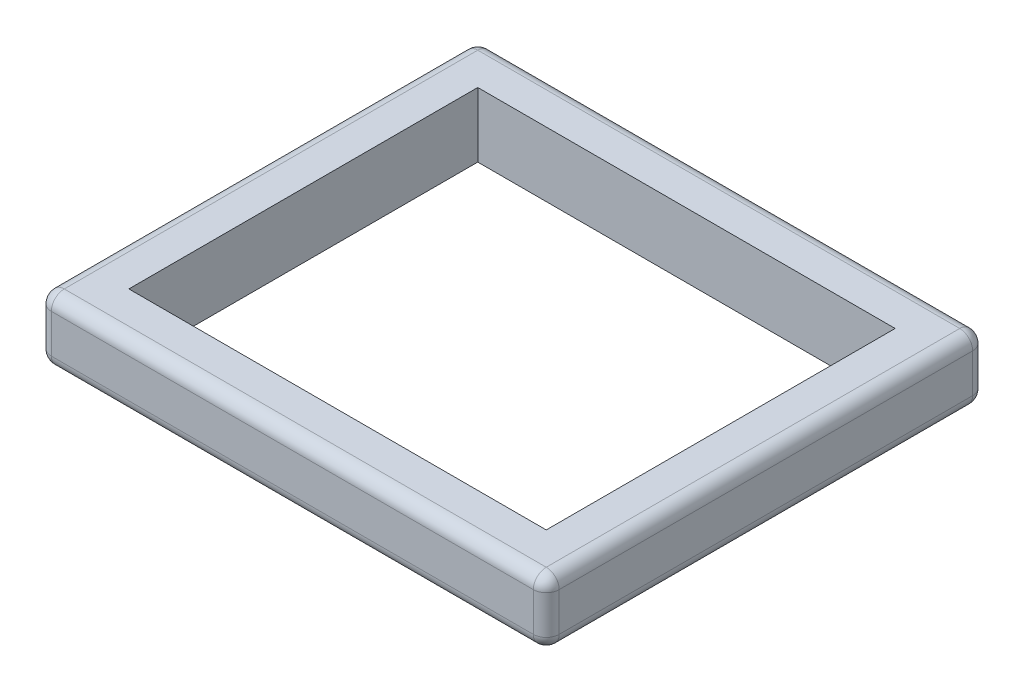
SolidWorks part; units mm, degrees
ref_plane "Front Plane" through (0, 0, 0) normal (0, 0, 1) x (1, 0, 0)
ref_plane "Top Plane" through (0, 0, 0) normal (0, 1, 0) x (1, 0, 0)
ref_plane "Right Plane" through (0, 0, 0) normal (1, 0, 0) x (0, 0, -1)
sketch "Sketch1" plane through (0, 0, 0) normal (0, 1, 0) x (1, 0, 0)
  line L0 (-272.9868, -413.7434) -> (-272.9868, 449.8566)
  line L1 (636.3332, -324.8434) -> (-184.0868, -324.8434)
  line L2 (636.3332, -324.8434) -> (636.3332, 360.9566)
  line L3 (636.3332, 360.9566) -> (-184.0868, 360.9566)
  line L4 (-184.0868, -324.8434) -> (-184.0868, 360.9566)
  line L5 (636.3332, -324.8434) -> (-184.0868, 360.9566) construction
  line L6 (636.3332, 360.9566) -> (-184.0868, -324.8434) construction
  line L7 (725.2332, 449.8566) -> (-272.9868, 449.8566)
  line L8 (725.2332, -413.7434) -> (725.2332, 449.8566)
  line L9 (725.2332, -413.7434) -> (-272.9868, -413.7434)
  point P0 (226.1232, 18.0566)
  dimension "D1" = 685.8
  dimension "D2" = 820.42
  dimension "D3" = 88.9
extrude "Boss-Extrude1" add sketch "Sketch1" along normal blind 127 contours L0 L7 L8 L9
sketch "Sketch2" plane through (0, 0, 0) normal (0, -1, 0) x (1, 0, 0)
  line L0 (725.2332, -449.8566) -> (-272.9868, -449.8566) construction
  line L1 (636.3332, -360.9566) -> (-184.0868, -360.9566)
  line L2 (636.3332, -360.9566) -> (636.3332, 324.8434)
  line L3 (636.3332, 324.8434) -> (-184.0868, 324.8434)
  line L4 (-184.0868, -360.9566) -> (-184.0868, 324.8434)
  line L5 (636.3332, -360.9566) -> (-184.0868, 324.8434) construction
  line L6 (636.3332, 324.8434) -> (-184.0868, -360.9566) construction
  line L7 (725.2332, 413.7434) -> (-272.9868, 413.7434) construction
  line L8 (-272.9868, 413.7434) -> (-272.9868, -449.8566) construction
  line L9 (725.2332, 413.7434) -> (725.2332, -449.8566) construction
  point P0 (226.1232, -18.0566)
  dimension "D1" = 88.9
  dimension "D2" = 88.9
  dimension "3" = 88.9
  dimension "D3" = 88.9
extrude "Cut-Extrude1" cut sketch "Sketch2" against normal blind 127
fillet "Fillet1" radius 25.4
